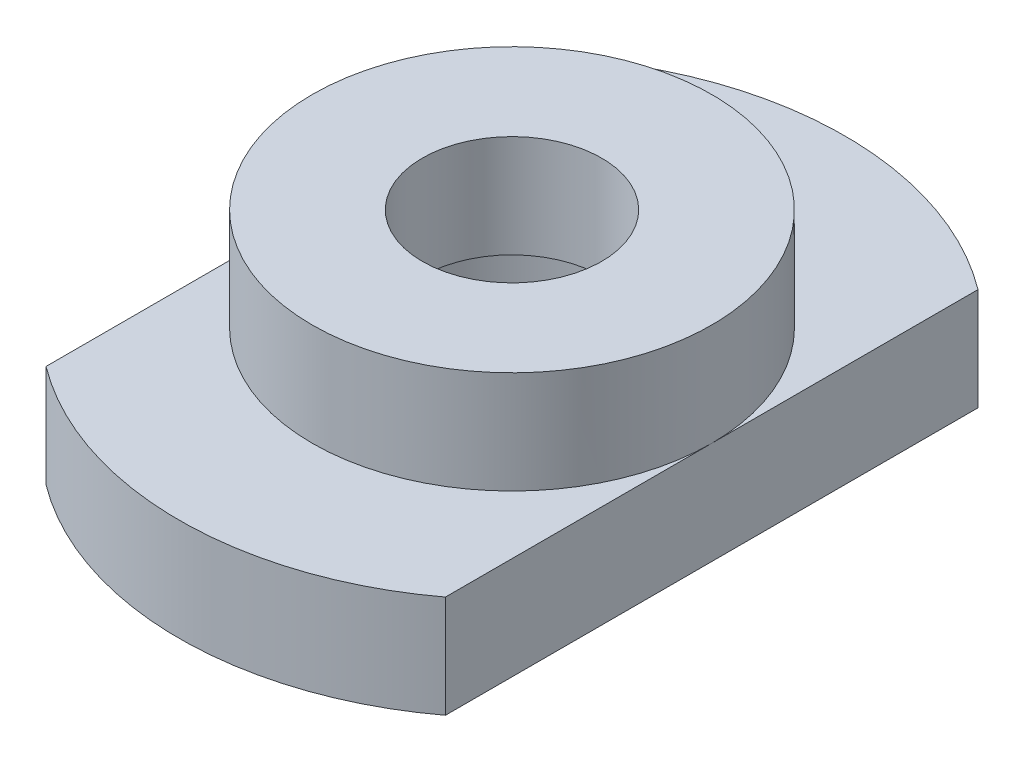
SolidWorks part; units mm, degrees
ref_plane "Front Plane" through (0, 0, 0) normal (0, 0, 1) x (1, 0, 0)
ref_plane "Top Plane" through (0, 0, 0) normal (0, 1, 0) x (1, 0, 0)
ref_plane "Right Plane" through (0, 0, 0) normal (1, 0, 0) x (0, 0, -1)
sketch "Sketch2" plane through (0, 0, 0) normal (0, 1, 0) x (1, 0, 0)
  line L1 (-2.9, 0) -> (2.9, 0)
  line L2 (-2.9, 0) -> (-2.9, 5)
  line L3 (-2.9, 5) -> (2.9, 5)
  line L4 (2.9, 0) -> (2.9, 5)
  line L5 (-2.9, 0) -> (2.9, 0)
  line L6 (-2.9, 0) -> (-2.9, -5)
  line L7 (-2.9, -5) -> (2.9, -5)
  line L8 (2.9, 0) -> (2.9, -5)
  line L9 (-3.9, 6) -> (3.9, 6)
  line L10 (-3.9, 6) -> (-3.9, -6)
  line L11 (-3.9, -6) -> (3.9, -6)
  line L12 (3.9, 6) -> (3.9, -6)
  circle A0 centre (0, 0) radius 2.9
  circle A1 centre (0, 0) radius 6.5
  dimension "D1" = 5.8
  dimension "D8" = 13
  dimension "D2" = 5
  dimension "D3" = 5
  dimension "D4" = 1
  dimension "D5" = 1
  dimension "D6" = 1
  dimension "D7" = 1
extrude "Boss-Extrude1" add sketch "Sketch2" along normal blind 2 contours L12 L9 L10 L11 L4 L8 L7 L6 L2 L3 | A0 L4 L3 L2 | A0 L6 L7 L8 | L11 A1 | L9 A1
sketch "Sketch3" plane through (0, 2, 0) normal (0, 1, 0) x (1, 0, 0)
  circle A0 centre (0, 0) radius 2.9
  circle A1 centre (0, 0) radius 1.75
  circle A2 centre (0, 0) radius 3.9
  circle M1 centre (0, 0) radius 2.9
  dimension "D1" = 3.5
extrude "Boss-Extrude2" add sketch "Sketch3" along normal blind 2 contours A2 M1 | A1 M1
